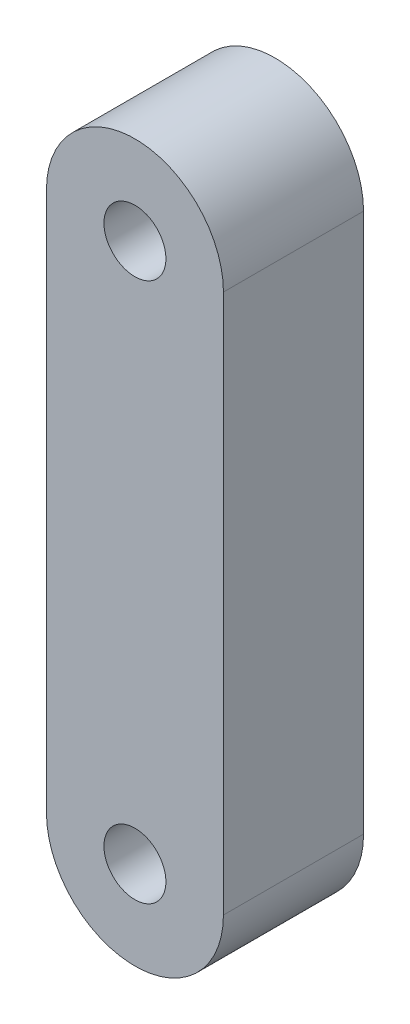
SolidWorks part; units mm, degrees
ref_plane "Plano frontal" through (0, 0, 0) normal (0, 0, 1) x (1, 0, 0)
ref_plane "Plano superior" through (0, 0, 0) normal (0, 1, 0) x (1, 0, 0)
ref_plane "Plano direito" through (0, 0, 0) normal (1, 0, 0) x (0, 0, -1)
ref_plane "Plano1" through (0, 0, 9.5) normal (0, 0, 1) x (1, 0, 0)
sketch "Esboço1" plane through (0, 0, 9.5) normal (0, 0, 1) x (1, 0, 0)
  line L0 (-77.6523, -56.6227) -> (-77.6523, -20.0448)
  line L1 (-89.6523, -20.0448) -> (-89.6523, -56.6227)
  circle A0 centre (-83.6523, -56.6227) radius 2.1
  circle A1 centre (-83.6523, -20.0448) radius 2.1
  arc A2 (-89.6523, -56.6227) -> (-77.6523, -56.6227) centre (-83.6523, -56.6227) ccw
  arc A3 (-77.6523, -20.0448) -> (-89.6523, -20.0448) centre (-83.6523, -20.0448) ccw
extrude "Ressalto-extrusão1" add sketch "Esboço1" against normal blind 9.5
